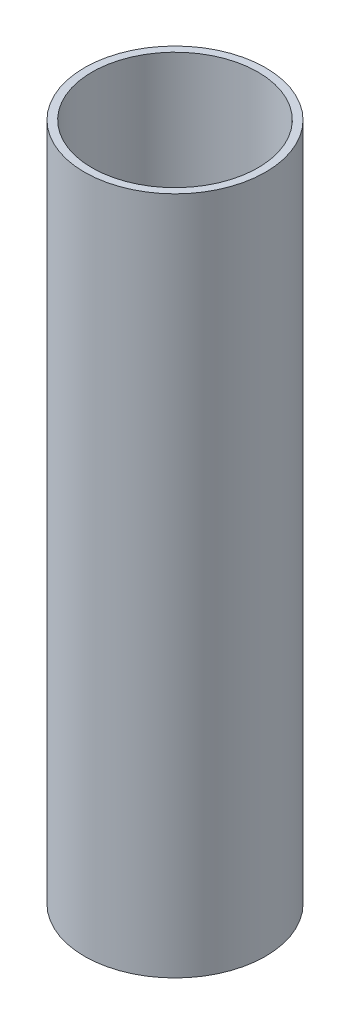
SolidWorks part; units mm, degrees
ref_plane "前基準面" through (0, 0, 0) normal (0, 0, 1) x (1, 0, 0)
ref_plane "上基準面" through (0, 0, 0) normal (0, 1, 0) x (1, 0, 0)
ref_plane "右基準面" through (0, 0, 0) normal (1, 0, 0) x (0, 0, -1)
sketch "草圖1" plane through (0, 0, 0) normal (0, 1, 0) x (1, 0, 0)
  circle A0 centre (0, 0) radius 24
  dimension "D1" = 48
extrude "填料-伸長1" add sketch "草圖1" along normal blind 180 contours A0
sketch "草圖2" plane through (0, 180, 0) normal (0, 1, 0) x (1, 0, 0)
  circle A0 centre (0, 0) radius 22
  dimension "D1" = 44
extrude "除料-伸長1" cut sketch "草圖2" against normal blind 180
ref_plane "平面1" through (-24, 0, 0) normal (1, 0, 0) x (0, 0, -1)
